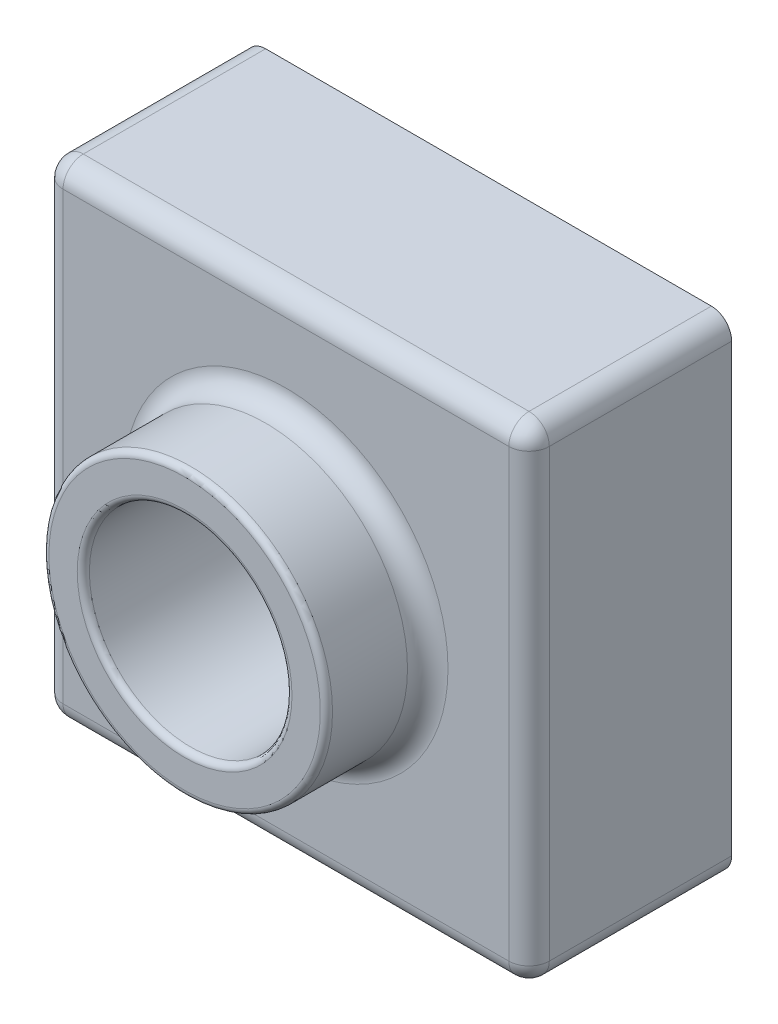
SolidWorks part; units mm, degrees
ref_plane "Front" through (0, 0, 0) normal (0, 0, 1) x (1, 0, 0)
ref_plane "Top" through (0, 0, 0) normal (0, 1, 0) x (1, 0, 0)
ref_plane "Right" through (0, 0, 0) normal (1, 0, 0) x (0, 0, -1)
sketch "Sketch1" plane through (0, 0, 0) normal (0, 1, 0) x (1, 0, 0)
  line L1 (0, 0) -> (120, 0)
  line L2 (0, 0) -> (0, 120)
  line L3 (0, 120) -> (120, 120)
  line L4 (120, 0) -> (120, 120)
  dimension "D1" = 120
  dimension "D2" = 120
extrude "Boss-Extrude1" add sketch "Sketch1" along normal blind 50
sketch "Sketch2" plane through (0, 50, 0) normal (0, 1, 0) x (1, 0, 0)
  line L0 (120, 0) -> (120, 120) construction
  line L1 (120, 120) -> (0, 120) construction
  circle A0 centre (60, 60) radius 35
  dimension "D3" = 70
  dimension "D1" = 60
  dimension "D2" = 60
extrude "Boss-Extrude2" add sketch "Sketch2" along normal blind 25
sketch "Sketch3" plane through (0, 75, 0) normal (0, 1, 0) x (1, 0, 0)
  circle A0 centre (60, 60) radius 25
  dimension "D1" = 50
extrude "Cut-Extrude1" cut sketch "Sketch3" against normal through all
fillet "Fillet2" radius 5 9 edges at (0, 25, -120) (120, 25, -120) (120, 25, 0) (0, 25, 0) (60, 50, -120) (0, 50, -60) (60, 50, 0) (120, 50, -60) (60, 50, -25)
fillet "Fillet3" radius 1.5 2 edges at (60, 75, -35) (60, 75, -25)
shell "Shell1" thickness 2
move or copy body "Body-Move/Copy1" bodies to move or copy 103 copy no rotation origin (60, 37.5, 0) rotation axis (0, 0, -1) rotation angle 90
move or copy body "Body-Move/Copy2" bodies to move or copy 104 copy no rotation origin (60, 0, -60) rotation axis (0, -1, 0) rotation angle 90
